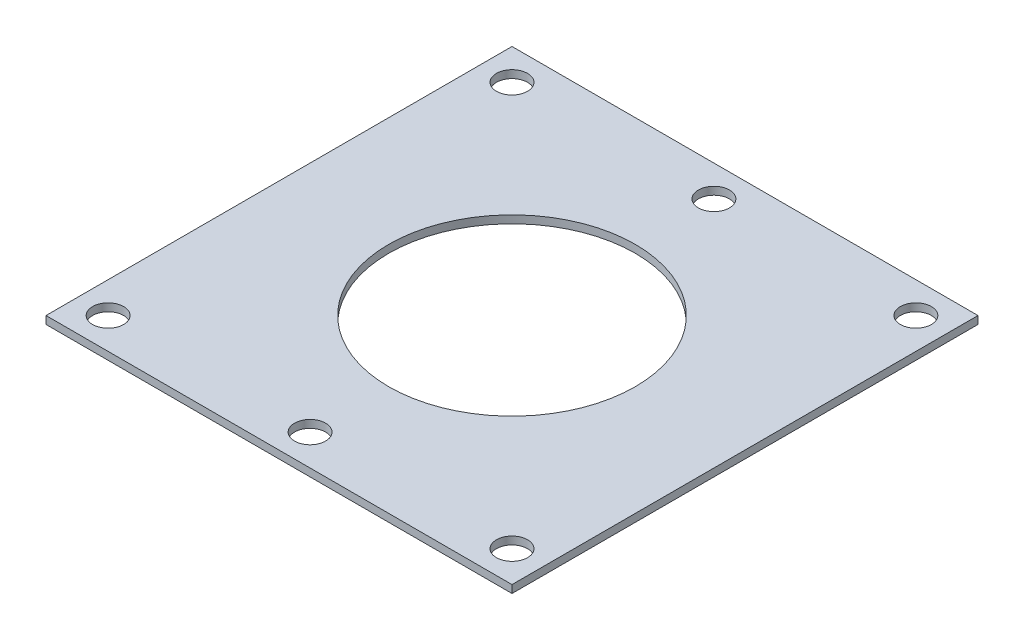
SolidWorks part; units mm, degrees
ref_plane "Front Plane" through (0, 0, 0) normal (0, 0, 1) x (1, 0, 0)
ref_plane "Top Plane" through (0, 0, 0) normal (0, 1, 0) x (1, 0, 0)
ref_plane "Right Plane" through (0, 0, 0) normal (1, 0, 0) x (0, 0, -1)
sketch "Sketch1" plane through (0, 0, 0) normal (0, 1, 0) x (1, 0, 0)
  line L1 (30, -30) -> (-30, -30)
  line L2 (30, -30) -> (30, 30)
  line L3 (30, 30) -> (-30, 30)
  line L4 (-30, -30) -> (-30, 30)
  line L5 (30, -30) -> (-30, 30) construction
  line L6 (30, 30) -> (-30, -30) construction
  point P0 (0, 0)
  dimension "D1" = 60
  dimension "D2" = 60
extrude "Boss-Extrude1" add sketch "Sketch1" along normal blind 1
sketch "Sketch2" plane through (0, 1, 0) normal (0, 1, 0) x (1, 0, 0)
  line L0 (30, 30) -> (-30, 30) construction
  line L2 (-30, 30) -> (-30, -30) construction
  line L3 (30, -30) -> (30, 30) construction
  line L5 (-30, -30) -> (30, -30) construction
  line L7 (-30, 30) -> (-30, -30) construction
  circle A0 centre (-26, 26) radius 2
  circle A1 centre (0, 26) radius 2
  circle A2 centre (26, 26) radius 2
  circle A3 centre (26, -26) radius 2
  circle A4 centre (0, -26) radius 2
  circle A5 centre (-26, -26) radius 2
  dimension "D1" = 4
  dimension "D5" = 4
  dimension "D7" = 4
  dimension "D10" = 4
  dimension "D16" = 4
  dimension "D17" = 4
  dimension "D2" = 4
  dimension "D3" = 4
  dimension "D4" = 4
  dimension "D6" = 0
  dimension "D8" = 4
  dimension "D9" = 4
  dimension "D11" = 4
  dimension "D12" = 4
  dimension "D13" = 4
  dimension "D14" = 4
  dimension "D15" = 4
  dimension "D18" = 0
extrude "Cut-Extrude1" cut sketch "Sketch2" against normal through all
sketch "Sketch4" plane through (0, 1, 0) normal (0, 1, 0) x (1, 0, 0)
  circle A0 centre (0, 0) radius 15.875
  dimension "D1" = 31.75
extrude "Cut-Extrude3" cut sketch "Sketch4" against normal blind 10
